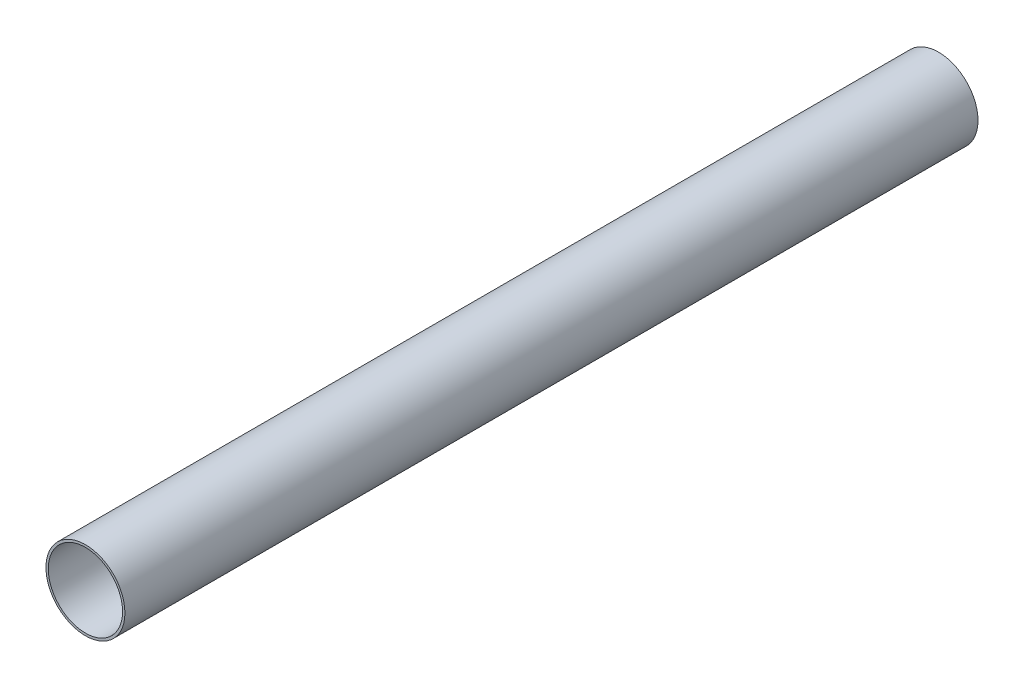
SolidWorks part; units mm, degrees
ref_plane "Front" through (0, 0, 0) normal (0, 0, 1) x (1, 0, 0)
ref_plane "Top" through (0, 0, 0) normal (0, 1, 0) x (1, 0, 0)
ref_plane "Side" through (0, 0, 0) normal (1, 0, 0) x (0, 0, -1)
sketch "PipeSketch" plane through (0, 0, 0) normal (0, 0, 1) x (1, 0, 0)
  circle A0 centre (0, 0) radius 254
  circle A1 centre (0, 0) radius 238.9124
  dimension "OuterDiameter" = 508
  dimension "InnerDiameter" = 477.8248
extrude "Extrusion" add sketch "PipeSketch" along normal blind 5486.4
sketch "FilterSketch" plane through (0, 0, 0) normal (0, 0, 1) x (1, 0, 0)
  circle A0 centre (0, 0) radius 254 construction
  dimension "NominalDiameter" = 508
